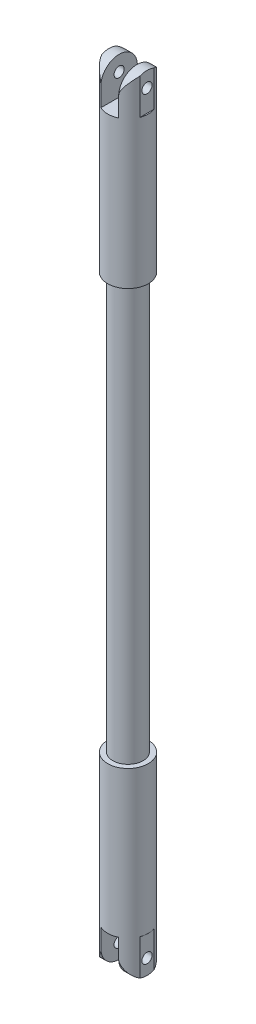
SolidWorks part; units mm, degrees
ref_plane "Front" through (0, 0, 0) normal (0, 0, 1) x (1, 0, 0)
ref_plane "Top" through (0, 0, 0) normal (0, 1, 0) x (1, 0, 0)
ref_plane "Right" through (0, 0, 0) normal (1, 0, 0) x (0, 0, -1)
sketch "Sketch1" plane through (0, 0, 0) normal (0, 0, 1) x (1, 0, 0)
  line L0 (0, -75) -> (0, 75)
  line L1 (0, 75) -> (-3, 75)
  line L2 (-3, 75) -> (-3, -35)
  line L3 (-3, -35) -> (-4, -35)
  line L4 (-4, -35) -> (-4, -75)
  line L5 (-4, -75) -> (0, -75)
  point P0 (-1.1071, 75)
  point P4 (0, 0)
  dimension "D1" = 150
  dimension "D2" = 4
  dimension "D3" = 3
  dimension "D4" = 40
revolve "Revolve1" add sketch "Sketch1" angle 360 about L0
sketch "Sketch2" plane through (0, 0, 0) normal (0, 0, 1) x (1, 0, 0)
  line L1 (1.75, -64) -> (-1.75, -64)
  line L2 (1.75, -64) -> (1.75, -86)
  line L3 (1.75, -86) -> (-1.75, -86)
  line L4 (-1.75, -64) -> (-1.75, -86)
  line L5 (1.75, -64) -> (-1.75, -86) construction
  line L6 (1.75, -86) -> (-1.75, -64) construction
  line L7 (-7.2391, -64) -> (-3.75, -64)
  line L8 (-7.2391, -64) -> (-7.2391, -74.8086)
  line L9 (-7.2391, -74.8086) -> (-3.75, -74.8086)
  line L10 (-3.75, -64) -> (-3.75, -74.8086)
  line L11 (3.75, -64) -> (8.854, -64)
  line L12 (3.75, -64) -> (3.75, -72.6694)
  line L13 (3.75, -72.6694) -> (8.854, -72.6694)
  line L14 (8.854, -64) -> (8.854, -72.6694)
  point P0 (0, -75)
  dimension "D1" = 3.5
  dimension "D2" = 22
  dimension "D3" = 2
  dimension "D4" = 2
extrude "Cut-Extrude1" cut sketch "Sketch2" against normal mid plane 20
sketch "Sketch3" plane through (3.75, 0, 0) normal (1, 0, 0) x (0, 0, -1)
  line L0 (0, -35) -> (0, -75) construction
  line L1 (1.3919, -64) -> (1.3919, -72.6694) construction
  circle A0 centre (0, -68.3347) radius 1
  point P6 (1.3919, -68.3347)
  dimension "D1" = 2
extrude "Cut-Extrude2" cut sketch "Sketch3" against normal through all both and the other way through all
sketch "Sketch4" plane through (3.75, 0, 0) normal (1, 0, 0) x (0, 0, -1)
  line L3 (-3.5969, -67.8288) -> (-5.6756, -67.8288)
  line L4 (-5.6756, -67.8288) -> (-5.6756, -76.9269)
  line L5 (-5.6756, -76.9269) -> (6.4072, -76.9269)
  line L6 (6.4072, -76.9269) -> (6.4072, -67.8288)
  line L7 (6.4072, -67.8288) -> (3.5969, -67.8288)
  line L8 (-3.5969, -64) -> (-3.5969, -75) construction
  arc A2 (-3.5969, -67.8288) -> (3.5969, -67.8288) centre (0, -67.7366) ccw
  point P6 (0, 0)
  point P8 (0, 0)
  point P9 (-3.5969, -67.8288)
extrude "Cut-Extrude3" cut sketch "Sketch4" against normal through all both and the other way through all
ref_plane "Plane1" through (0, 6, 0) normal (0, 1, 0) x (1, 0, 0)
split "Split1" trim tools "Plane1" bodies to split 104 resulting bodies 109
mirror "Mirror1" about plane through (0, 6, 0) normal (0, 1, 0) of bodies 109 104
